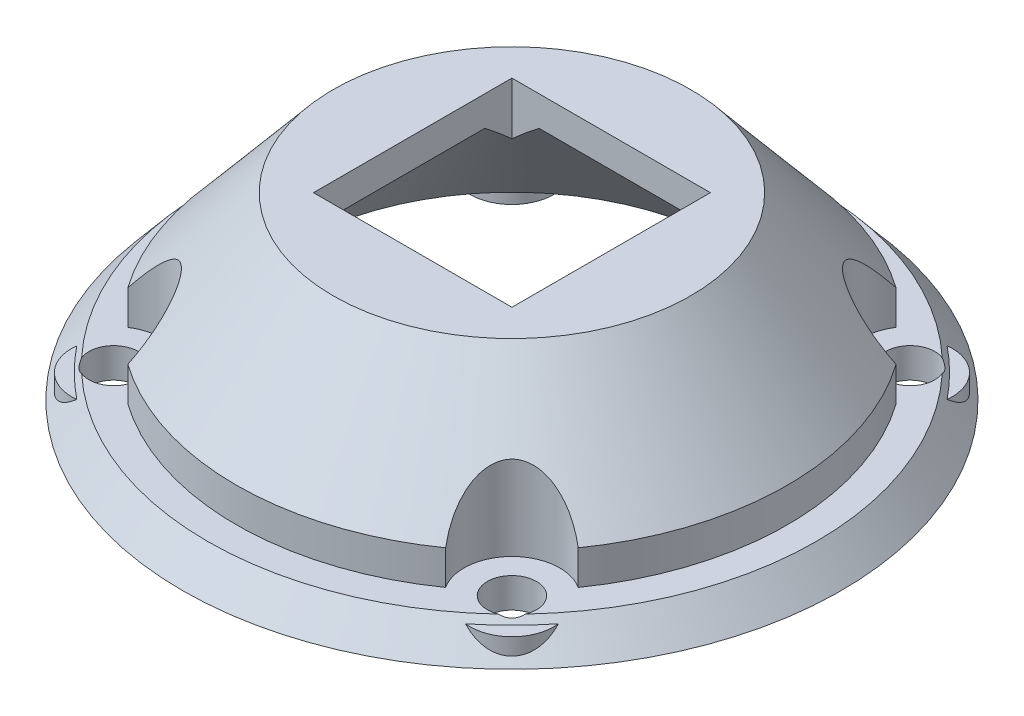
SolidWorks part; units mm, degrees
ref_plane "Спереди" through (0, 0, 0) normal (0, 0, 1) x (1, 0, 0)
ref_plane "Сверху" through (0, 0, 0) normal (0, 1, 0) x (1, 0, 0)
ref_plane "Справа" through (0, 0, 0) normal (1, 0, 0) x (0, 0, -1)
sketch "Sketch1" plane through (0, 0, 0) normal (0, 1, 0) x (1, 0, 0)
  circle A0 centre (0, 0) radius 55
  dimension "D1" = 110
extrude "Boss-Extrude1" add sketch "Sketch1" along normal blind 30 draft 40
sketch "Sketch2" plane through (0, 0, 0) normal (0, -1, 0) x (1, 0, 0)
  circle A0 centre (0, 0) radius 40
  dimension "D1" = 80
extrude "Cut-Extrude2" cut sketch "Sketch2" against normal through all draft 38
sketch "Sketch3" plane through (0, 0, 0) normal (0, -1, 0) x (1, 0, 0)
  line L1 (-33.234, -33.234) -> (33.234, -33.234) construction
  line L2 (-33.234, -33.234) -> (-33.234, 33.234) construction
  line L3 (-33.234, 33.234) -> (33.234, 33.234) construction
  line L4 (33.234, -33.234) -> (33.234, 33.234) construction
  line L5 (-33.234, -33.234) -> (33.234, 33.234) construction
  line L6 (-33.234, 33.234) -> (33.234, -33.234) construction
  circle A0 centre (0, 0) radius 47 construction
  circle A1 centre (0, 0) radius 55 construction
  circle A2 centre (33.234, 33.234) radius 4.1
  circle A3 centre (33.234, -33.234) radius 4.1
  circle A4 centre (-33.234, -33.234) radius 4.1
  circle A5 centre (-33.234, 33.234) radius 4.1
  dimension "D1" = 8
  dimension "D2" = 8.2
extrude "Cut-Extrude3" cut sketch "Sketch3" against normal through all
sketch "Sketch4" plane through (0, 0, 0) normal (0, -1, 0) x (1, 0, 0)
  circle A0 centre (33.234, 33.234) radius 8
  circle A1 centre (33.234, -33.234) radius 8
  circle A2 centre (-33.234, -33.234) radius 8
  circle A3 centre (-33.234, 33.234) radius 8
  dimension "D1" = 16
extrude "Cut-Extrude4" cut sketch "Sketch4" against normal through all from offset 5 offset against normal yes
sketch "Sketch5" plane through (0, 0, 0) normal (0, -1, 0) x (1, 0, 0)
  circle A0 centre (0, 0) radius 46
  dimension "D1" = 92
extrude "Cut-Extrude5" cut sketch "Sketch5" against normal through all from offset 5 flip side to cut offset against normal yes
sketch "Sketch6" plane through (0, 0, 0) normal (0, -1, 0) x (1, 0, 0)
  circle A0 centre (0, 0) radius 50
  dimension "D1" = 100
extrude "Cut-Extrude6" cut sketch "Sketch6" against normal blind 4
sketch "Sketch7" plane through (0, 30, 0) normal (0, 1, 0) x (1, 0, 0)
  line L1 (-16.5614, 16.5614) -> (16.5614, 16.5614)
  line L2 (-16.5614, 16.5614) -> (-16.5614, -16.5614)
  line L3 (-16.5614, -16.5614) -> (16.5614, -16.5614)
  line L4 (16.5614, 16.5614) -> (16.5614, -16.5614)
  line L5 (-16.5614, 16.5614) -> (16.5614, -16.5614) construction
  line L6 (-16.5614, -16.5614) -> (16.5614, 16.5614) construction
  circle A0 centre (0, 0) radius 16.5614 construction
sketch "Sketch8" plane through (0, 4, 0) normal (0, -1, 0) x (1, 0, 0)
  circle A0 centre (33.234, -33.234) radius 7
  circle A1 centre (33.234, -33.234) radius 4.1
  circle A2 centre (-33.234, -33.234) radius 4.1
  circle A3 centre (-33.234, -33.234) radius 7
  circle A4 centre (-33.234, 33.234) radius 7
  circle A5 centre (-33.234, 33.234) radius 4.1
  circle A6 centre (33.234, 33.234) radius 7
  circle A7 centre (33.234, 33.234) radius 4.1
  dimension "D1" = 14
  dimension "D2" = 8.2
extrude "Boss-Extrude3" add sketch "Sketch8" along normal up to surface (4 mm away) up to face at (0, 0, 0)
extrude "Cut-Extrude7" cut sketch "Sketch7" against normal through all
sketch "Sketch9" plane through (0, 30, 0) normal (0, 1, 0) x (1, 0, 0)
  line L1 (-16.5614, 16.5614) -> (16.5614, 16.5614)
  line L2 (-16.5614, 16.5614) -> (-16.5614, -16.5614)
  line L3 (-16.5614, -16.5614) -> (16.5614, -16.5614)
  line L4 (16.5614, 16.5614) -> (16.5614, -16.5614)
  line L5 (-16.5614, 16.5614) -> (16.5614, -16.5614) construction
  line L6 (-16.5614, -16.5614) -> (16.5614, 16.5614) construction
  circle A0 centre (0, 0) radius 29.827
  point P0 (0, 0)
extrude "Boss-Extrude4" add sketch "Sketch9" against normal blind 5
